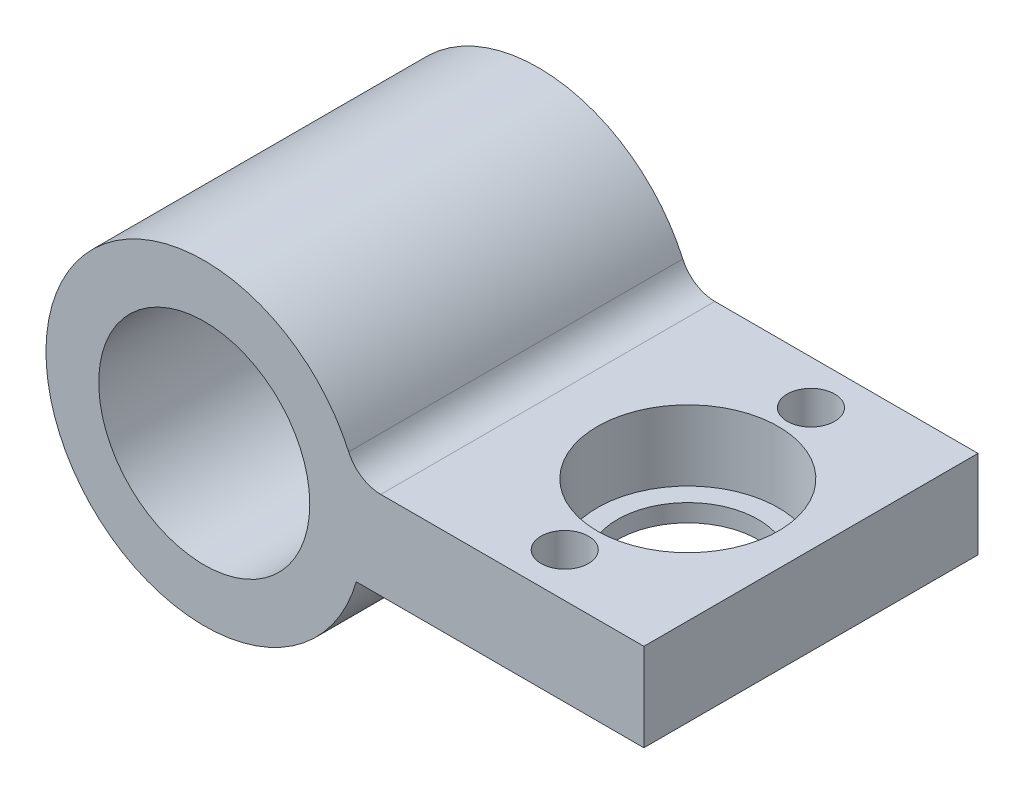
SolidWorks part; units mm, degrees
ref_plane "Front Plane" through (0, 0, 0) normal (0, 0, 1) x (1, 0, 0)
ref_plane "Top Plane" through (0, 0, 0) normal (0, 1, 0) x (1, 0, 0)
ref_plane "Right Plane" through (0, 0, 0) normal (1, 0, 0) x (0, 0, -1)
sketch "Sketch1" plane through (0, 0, 0) normal (0, 0, 1) x (1, 0, 0)
  circle A0 centre (0, 0) radius 6
  circle A1 centre (0, 0) radius 9
  dimension "D1" = 18
  dimension "D2" = 12
extrude "Main" add sketch "Sketch1" along normal mid plane 19
sketch "Sketch2" plane through (0, 0, 0) normal (0, 1, 0) x (1, 0, 0)
  line L0 (9, 9.5) -> (-9, 9.5) construction
  line L1 (0, 9.5) -> (25, 9.5)
  line L2 (0, 9.5) -> (0, -9.5)
  line L3 (0, -9.5) -> (25, -9.5)
  line L4 (25, 9.5) -> (25, -9.5)
  line L5 (-9, -9.5) -> (9, -9.5) construction
  line L7 (18, 7) -> (18, -7) construction
  circle A0 centre (18, 0) radius 4
  circle A1 centre (18, 7) radius 1.35
  circle A2 centre (18, -7) radius 1.35
  dimension "D4" = 8
  dimension "D5" = 2.7
  dimension "D2" = 25
  dimension "D3" = 7
  dimension "D6" = 14
extrude "BallSupportExtrusion" add sketch "Sketch2" along normal mid plane 5
sketch "Sketch3" plane through (0, 2.5, 0) normal (0, 1, 0) x (1, 0, 0)
  circle A0 centre (18, 0) radius 5.15
  dimension "D1" = 10.3
extrude "BallSupportHole" cut sketch "Sketch3" against normal blind 4
fillet "Fillet2" radius 2 1 edges at (8.6458, 2.5, 0)
sketch "Sketch5" plane through (0, 0, 9.5) normal (0, 0, 1) x (1, 0, 0)
  circle A0 centre (0, 0) radius 6
  dimension "D1" = 12
extrude "Cut-Extrude2" cut sketch "Sketch5" against normal through all
